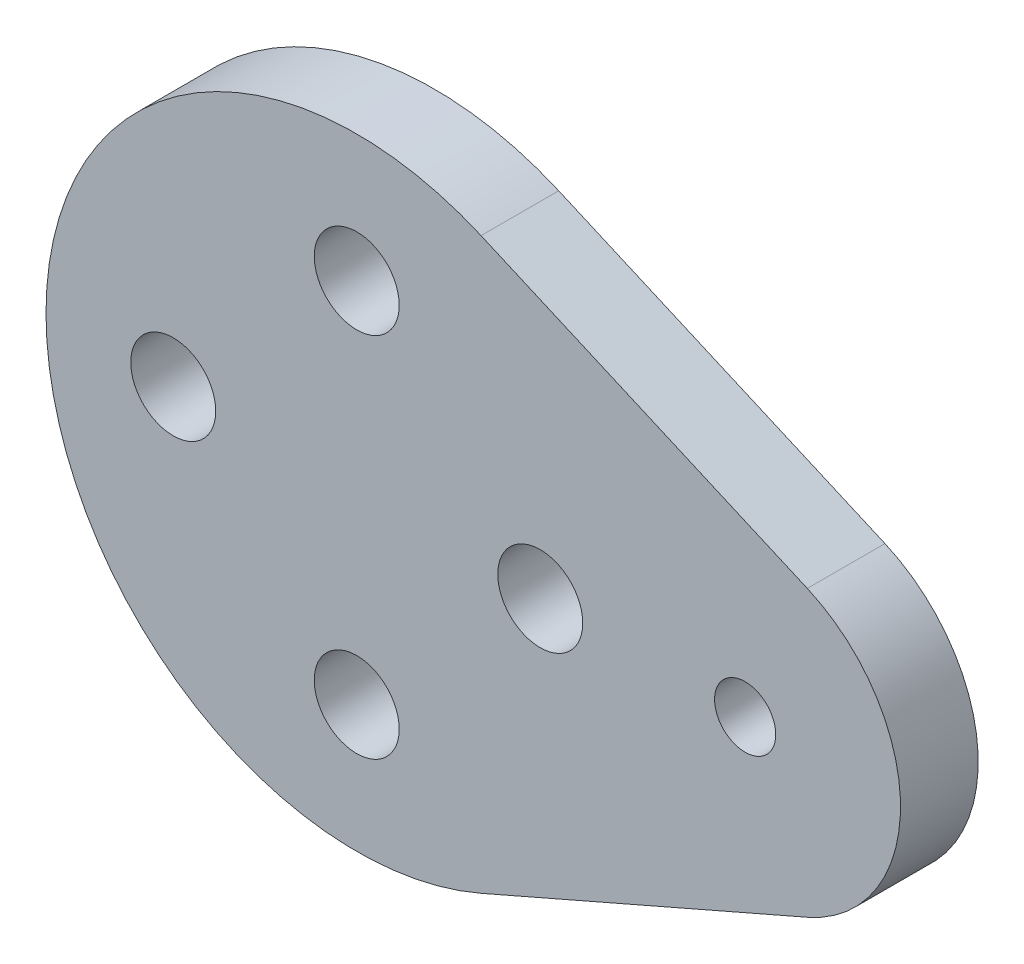
SolidWorks part; units mm, degrees
ref_plane "Front Plane" through (0, 0, 0) normal (0, 0, 1) x (1, 0, 0)
ref_plane "Top Plane" through (0, 0, 0) normal (0, 1, 0) x (1, 0, 0)
ref_plane "Right Plane" through (0, 0, 0) normal (1, 0, 0) x (0, 0, -1)
sketch "Sketch2" plane through (0, 0, 0) normal (0, 0, 1) x (1, 0, 0)
  circle A11 centre (0, 0) radius 8.9
  circle A12 centre (0, 0) radius 8.7
  circle A13 centre (0, -6) radius 2
  circle A14 centre (0, -6) radius 2.5
  circle A15 centre (6, 0) radius 2.5
  circle A16 centre (6, 0) radius 2
  circle A17 centre (0, 0) radius 2.8
  circle A18 centre (0, 6) radius 2
  circle A19 centre (0, 6) radius 2.5
  circle A20 centre (-6, 0) radius 2.5
  circle A21 centre (-6, 0) radius 2
sketch "Sketch1" plane through (0, 0, 0) normal (0, 0, 1) x (1, 0, 0)
  line L2 (0, 0) -> (12.7, 0) construction
  line L3 (4.064, 9.3118) -> (14.732, 4.6559)
  line L4 (14.732, -4.6559) -> (4.064, -9.3118)
  circle A0 centre (0, 6) radius 1.3891
  circle A1 centre (6, 0) radius 1.3891
  circle A2 centre (12.7, 0) radius 1
  arc A3 (14.732, -4.6559) -> (14.732, 4.6559) centre (12.7, 0) ccw
  arc A4 (4.064, 9.3118) -> (4.064, -9.3118) centre (0, 0) ccw
  circle A5 centre (0, -6) radius 1.3891
  circle A6 centre (-6, 0) radius 1.3891
  point P20 (0, 0)
  dimension "D1" = 5.08
  dimension "D2" = 2.7781
  dimension "D4" = 20.32
  dimension "D6" = 2
  dimension "D3" = 12.7
  dimension "D5" = 4
extrude "Boss-Extrude1" add sketch "Sketch1" along normal blind 2.54
